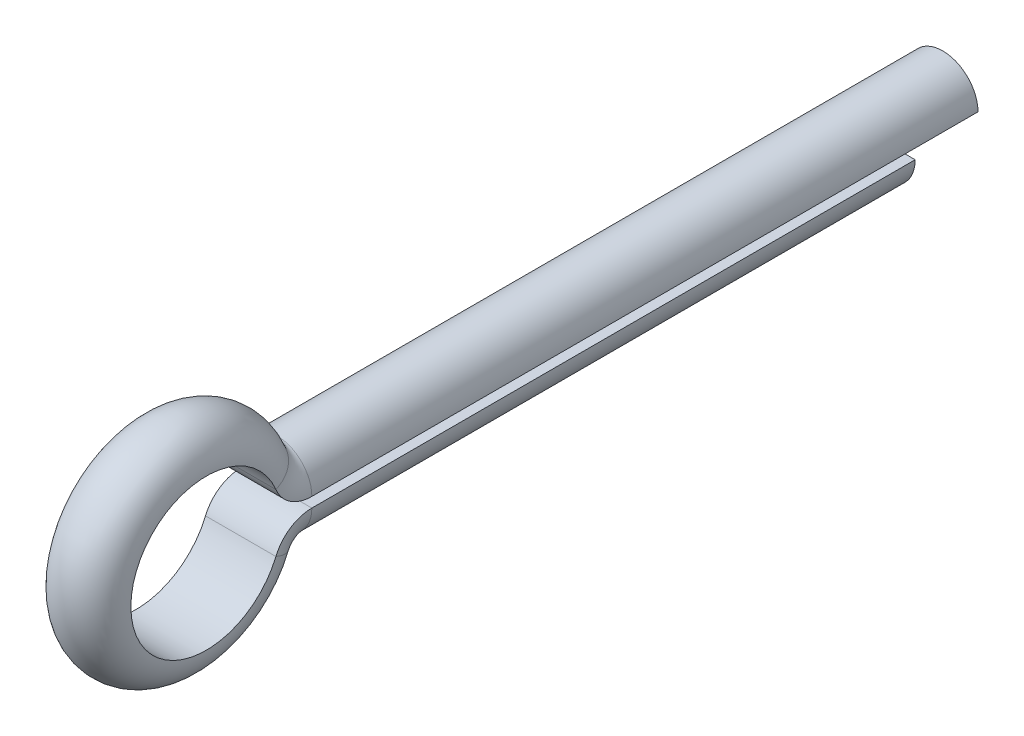
SolidWorks part; units mm, degrees
material "1.0545 (S355N)"
ref_plane "Płaszczyzna przednia" through (0, 0, 0) normal (0, 0, 1) x (1, 0, 0)
ref_plane "Płaszczyzna górna" through (0, 0, 0) normal (0, 1, 0) x (1, 0, 0)
ref_plane "Płaszczyzna prawa" through (0, 0, 0) normal (1, 0, 0) x (0, 0, -1)
sketch "Szkic1" plane through (0, 0, 0) normal (1, 0, 0) x (0, 0, -1)
  line L0 (0, 0) -> (-12, 0)
  arc A2 (-15.5, 0) -> (-12.8077, -0.5385) centre (-14.1, 0) ccw
  arc A4 (-12.8077, -0.5385) -> (-12, 0) centre (-12, -0.875) cw
  dimension "D1" = 1.4
  dimension "D3" = 15.5
  dimension "D2" = 12
sketch "Szkic2" plane through (0, 0, 0) normal (0, 0, 1) x (1, 0, 0)
  line L0 (0, -1.4) -> (0, 0) construction
  line L1 (-0.7, -0.1) -> (0.7, -0.1)
  arc A0 (-0.7, -0.1) -> (0.7, -0.1) centre (0, -0.1) ccw
  dimension "D1" = 0.7
  dimension "D2" = 0.1
sweep "Wyciągnięcie po ścieżce1" add profiles "Szkic2" path "Szkic1"
mirror "Lustro1" about plane through (0, 0, 0) normal (0, 1, 0) of "Wyciągnięcie po ścieżce1"
sketch "Szkic3" plane through (0, 0, 0) normal (0, 0, -1) x (-1, 0, 0)
  line L0 (0.7, 0.1) -> (-0.7, 0.1) construction
  line L1 (0.7, 0.1) -> (-0.7, 0.1)
  arc A0 (0.7, 0.1) -> (-0.7, 0.1) centre (0, 0.1) ccw construction
  arc A1 (0.7, 0.1) -> (-0.7, 0.1) centre (0, 0.1) ccw
extrude "Dodanie-wyciągnięcie1" add sketch "Szkic3" along normal blind 1.25
